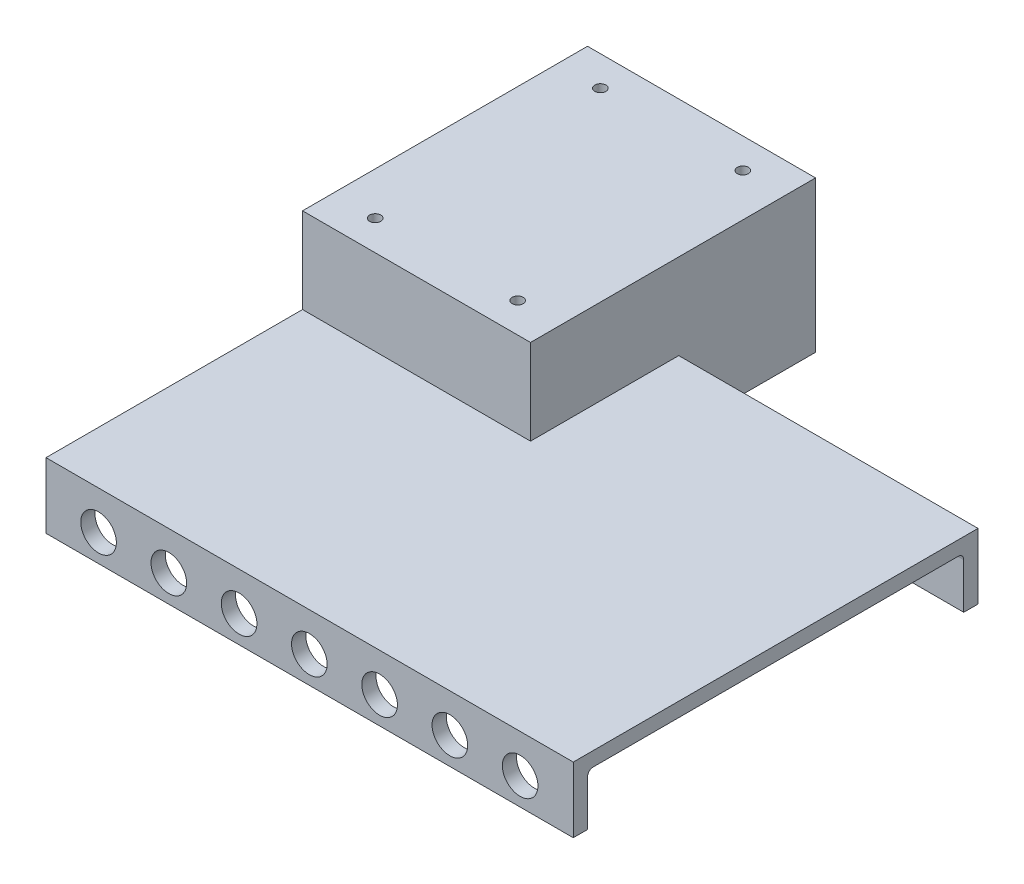
SolidWorks part; units mm, degrees
ref_plane "Front Plane" through (0, 0, 0) normal (0, 0, 1) x (1, 0, 0)
ref_plane "Top Plane" through (0, 0, 0) normal (0, 1, 0) x (1, 0, 0)
ref_plane "Right Plane" through (0, 0, 0) normal (1, 0, 0) x (0, 0, -1)
sketch "Sketch1" plane through (0, 0, 0) normal (0, 1, 0) x (1, 0, 0)
  line L1 (0, 0) -> (185, 0)
  line L2 (0, 0) -> (0, 142)
  line L3 (0, 142) -> (185, 142)
  line L4 (185, 0) -> (185, 142)
  dimension "D1" = 185
  dimension "D2" = 142
extrude "Boss-Extrude1" add sketch "Sketch1" along normal blind 23
sketch "Sketch12" plane through (0, 0, 0) normal (0, 1, 0) x (1, 0, 0)
  line L1 (0, 90) -> (80, 90)
  line L2 (0, 90) -> (0, 190)
  line L3 (0, 190) -> (80, 190)
  line L4 (80, 90) -> (80, 190)
  dimension "D1" = 90
  dimension "D2" = 80
  dimension "D3" = 100
extrude "Boss-Extrude6" add sketch "Sketch12" along normal blind 53
shell "Shell1" thickness 5
sketch "Sketch11" plane through (0, 0, 0) normal (0, 0, 1) x (1, 0, 0)
  line L0 (0, 23) -> (0, 0) construction
  line L3 (0, 23) -> (185, 23) construction
  circle A6 centre (18.4375, 9.5) radius 6.25
  circle A7 centre (43.0889, 9.5) radius 6.25
  circle A8 centre (67.7402, 9.5) radius 6.25
  circle A9 centre (92.3916, 9.5) radius 6.25
  circle A10 centre (117.0429, 9.5) radius 6.25
  circle A11 centre (141.6943, 9.5) radius 6.25
  circle A12 centre (166.3456, 9.5) radius 6.25
  dimension "D1" = 12.5
  dimension "D2" = 18.4375
  dimension "D4" = 24.6514
  dimension "D5" = 13.5
  dimension "D3" = 7
extrude "Cut-Extrude2" cut sketch "Sketch11" against normal blind 6
fillet "Fillet1" radius 2 5 edges at (92.5, 18, -5) (130, 18, -137) (75, 48, -140) (37.5, 48, -95) (37.5, 48, -185)
sketch "Sketch13" plane through (0, 53, 0) normal (0, 1, 0) x (1, 0, 0)
  line L1 (0, 140) -> (80, 140) construction
  line L2 (0, 90) -> (0, 190) construction
  line L3 (80, 90) -> (80, 190) construction
  line L4 (40, 190) -> (40, 90) construction
  line L5 (0, 190) -> (80, 190) construction
  line L6 (0, 90) -> (80, 90) construction
  circle A0 centre (15, 100.5) radius 1.95
  circle A1 centre (15, 179.5) radius 1.95
  circle A2 centre (65, 179.5) radius 1.95
  circle A3 centre (65, 100.5) radius 1.95
  dimension "D1" = 3.9
  dimension "D2" = 79
  dimension "D3" = 50
extrude "Cut-Extrude3" cut sketch "Sketch13" against normal through all
